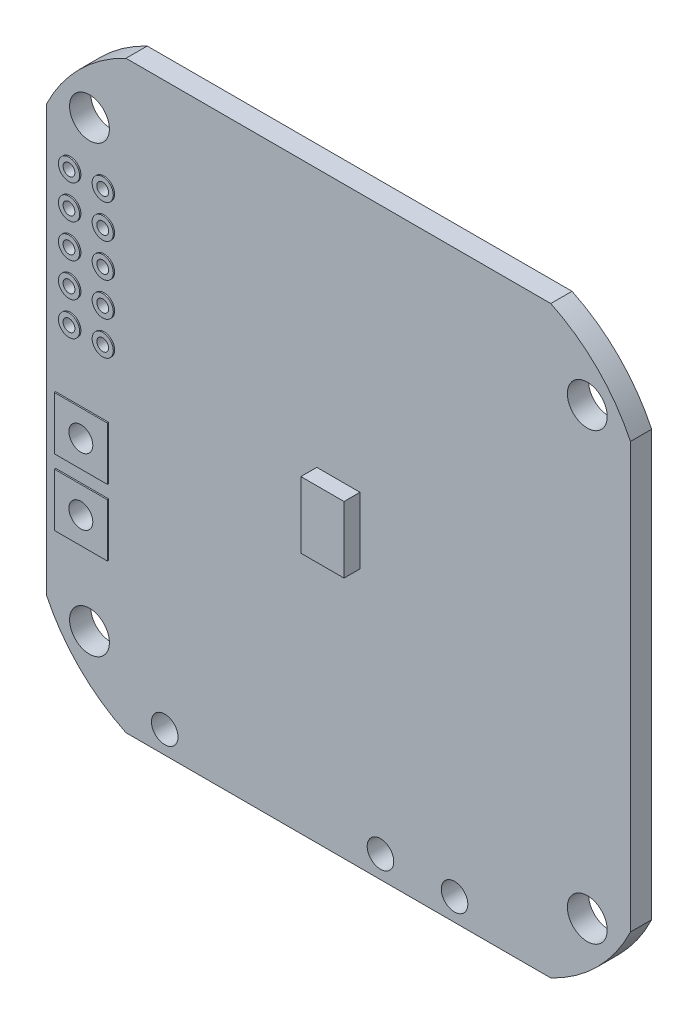
SolidWorks part; units mm, degrees
material "6061-T6 (SS)"
ref_plane "Alzado" through (0, 0, 0) normal (0, 0, 1) x (1, 0, 0)
ref_plane "Planta" through (0, 0, 0) normal (0, 1, 0) x (1, 0, 0)
ref_plane "Vista lateral" through (0, 0, 0) normal (1, 0, 0) x (0, 0, -1)
sketch "Croquis1" plane through (0, 0, 0) normal (0, 0, 1) x (1, 0, 0)
  line L0 (-22, 16) -> (-22, -16)
  line L1 (0, 0) -> (0, -6.2515) construction
  line L2 (22, 16) -> (22, -16)
  line L3 (-16, -22) -> (16, -22)
  line L4 (0, 0) -> (8.2976, 0) construction
  line L5 (-16, 22) -> (16, 22)
  arc A0 (-16, 22) -> (-22, 16) centre (-10.4982, 10.4982) ccw
  arc A2 (16, -22) -> (22, -16) centre (10.4982, -10.4982) ccw
  arc A3 (-22, -16) -> (-16, -22) centre (-10.4982, -10.4982) ccw
  arc A7 (22, 16) -> (16, 22) centre (10.4982, 10.4982) ccw
  point P0 (0, 0)
  point P4 (-22, 0)
  point P13 (0, -22)
  dimension "D3" = 25.5
  dimension "D4" = 32
  dimension "D1" = 32
  dimension "D2" = 22
  dimension "D5" = 22
extrude "Saliente-Extruir1" add sketch "Croquis1" along normal mid plane 1.6
sketch "Croquis2" plane through (0, 0, 0.8) normal (0, 0, 1) x (1, 0, 0)
  line L1 (18.75, -16.75) -> (-18.75, -16.75) construction
  line L2 (18.75, -16.75) -> (18.75, 16.75) construction
  line L3 (18.75, 16.75) -> (-18.75, 16.75) construction
  line L4 (-18.75, -16.75) -> (-18.75, 16.75) construction
  line L5 (18.75, -16.75) -> (-18.75, 16.75) construction
  line L6 (18.75, 16.75) -> (-18.75, -16.75) construction
  circle A0 centre (-18.75, 16.75) radius 1.5
  circle A1 centre (18.75, 16.75) radius 1.5
  circle A2 centre (18.75, -16.75) radius 1.5
  circle A3 centre (-18.75, -16.75) radius 1.5
  point P0 (0, 0)
  dimension "D1" = 3
  dimension "D2" = 37.5
  dimension "D3" = 33.5
extrude "Cortar-Extruir1" cut sketch "Croquis2" against normal through all
sketch "Croquis3" plane through (0, 0, 0.8) normal (0, 0, 1) x (1, 0, 0)
  line L1 (-1.625, 2.5) -> (1.625, 2.5)
  line L2 (-1.625, 2.5) -> (-1.625, -2.5)
  line L3 (-1.625, -2.5) -> (1.625, -2.5)
  line L4 (1.625, 2.5) -> (1.625, -2.5)
  line L5 (-1.625, 2.5) -> (1.625, -2.5) construction
  line L6 (-1.625, -2.5) -> (1.625, 2.5) construction
  point P0 (0, 0)
  dimension "D1" = 5
  dimension "D2" = 3.25
extrude "Saliente-Extruir2" add sketch "Croquis3" along normal blind 1.2
sketch "Croquis4" plane through (0, 0, -0.8) normal (0, 0, -1) x (-1, 0, 0)
  line L0 (22, 16) -> (22, -16) construction
  line L1 (-16, 22) -> (16, 22) construction
  circle A0 centre (17.653, 12.7) radius 0.445
  circle A1 centre (20.193, 12.7) radius 0.445
  circle A2 centre (20.193, 10.16) radius 0.445
  circle A3 centre (20.193, 7.62) radius 0.445
  circle A4 centre (20.193, 5.08) radius 0.445
  circle A5 centre (20.193, 2.54) radius 0.445
  circle A6 centre (17.653, 10.16) radius 0.445
  circle A7 centre (17.653, 7.62) radius 0.445
  circle A8 centre (17.653, 5.08) radius 0.445
  circle A9 centre (17.653, 2.54) radius 0.445
  dimension "D1" = 0.89
  dimension "D3" = 1.807
  dimension "D4" = 9.3
  dimension "D2" = 5
extrude "Cortar-Extruir2" cut sketch "Croquis4" against normal through all
sketch "Croquis5" plane through (0, 0, 0) normal (0, 0, 1) x (1, 0, 0)
  line L0 (-16, -22) -> (16, -22) construction
  line L1 (-17.3, -2.4) -> (-21.3, -2.4)
  line L2 (-17.3, -2.4) -> (-17.3, -6.4)
  line L3 (-17.3, -6.4) -> (-21.3, -6.4)
  line L4 (-21.3, -2.4) -> (-21.3, -6.4)
  line L5 (-17.3, -2.4) -> (-21.3, -6.4) construction
  line L6 (-17.3, -6.4) -> (-21.3, -2.4) construction
  line L7 (-17.3, -7.4) -> (-21.3, -7.4)
  line L8 (-17.3, -7.4) -> (-17.3, -11.4)
  line L9 (-17.3, -11.4) -> (-21.3, -11.4)
  line L10 (-21.3, -7.4) -> (-21.3, -11.4)
  line L11 (-17.3, -7.4) -> (-21.3, -11.4) construction
  line L12 (-17.3, -11.4) -> (-21.3, -7.4) construction
  line L13 (-22, 16) -> (-22, -16) construction
  circle A0 centre (-17.653, 2.54) radius 0.7974
  circle A1 centre (-20.193, 2.54) radius 0.7974
  circle A2 centre (-20.193, 5.08) radius 0.7974
  circle A3 centre (-17.653, 5.08) radius 0.7974
  circle A4 centre (-17.653, 7.62) radius 0.7974
  circle A5 centre (-17.653, 10.16) radius 0.7974
  circle A6 centre (-20.193, 7.62) radius 0.7974
  circle A7 centre (-20.193, 10.16) radius 0.7974
  circle A8 centre (-17.653, 12.7) radius 0.7974
  circle A9 centre (-20.193, 12.7) radius 0.7974
  circle A10 centre (-17.653, 12.7) radius 0.445
  circle A11 centre (-20.193, 12.7) radius 0.445
  circle A12 centre (-20.193, 10.16) radius 0.445
  circle A13 centre (-17.653, 10.16) radius 0.445
  circle A14 centre (-17.653, 7.62) radius 0.445
  circle A15 centre (-20.193, 7.62) radius 0.445
  circle A16 centre (-20.193, 5.08) radius 0.445
  circle A17 centre (-17.653, 5.08) radius 0.445
  circle A18 centre (-17.653, 2.54) radius 0.445
  circle A19 centre (-20.193, 2.54) radius 0.445
  point P0 (-19.3, -4.4)
  point P5 (-19.3, -9.4)
  dimension "D1" = 4
  dimension "D2" = 4
  dimension "D3" = 5
  dimension "D4" = 4
  dimension "D5" = 4
  dimension "D6" = 12.6
  dimension "D7" = 2.7
extrude "Saliente-Extruir3" add sketch "Croquis5" along normal mid plane 1.8
sketch "Croquis6" plane through (0, 0, -0.9) normal (0, 0, -1) x (-1, 0, 0)
  line L0 (21.3, -2.4) -> (21.3, -6.4) construction
  line L1 (21.3, -7.4) -> (21.3, -11.4) construction
  circle A0 centre (19.3, -4.4) radius 0.9
  circle A1 centre (19.3, -9.4) radius 0.9
  point P6 (21.3, -4.4)
  point P9 (21.3, -9.4)
  dimension "D1" = 1.8
extrude "Cortar-Extruir3" cut sketch "Croquis6" against normal through all both and the other way through all
sketch "Croquis7" plane through (0, 0, -0.8) normal (0, 0, -1) x (-1, 0, 0)
  line L0 (16, -22) -> (-16, -22) construction
  line L1 (22, 16) -> (22, -16) construction
  circle A0 centre (-8.75, -20.32) radius 1
  circle A1 centre (-3.17, -20.32) radius 1
  circle A2 centre (13.08, -20.32) radius 1
  dimension "D1" = 2
  dimension "D2" = 1.68
  dimension "D3" = 5.58
  dimension "D4" = 16.25
  dimension "D5" = 8.92
extrude "Cortar-Extruir4" cut sketch "Croquis7" against normal blind 10
sketch "Croquis8" plane through (0, 0, -0.8) normal (0, 0, -1) x (-1, 0, 0)
  line L0 (-22, -16) -> (-22, 16) construction
  line L1 (-20.5, 13.185) -> (-17.5, 13.185)
  line L2 (-20.5, 13.185) -> (-20.5, 10.685)
  line L3 (-20.5, 10.685) -> (-17.5, 10.685)
  line L4 (-17.5, 13.185) -> (-17.5, 10.685)
  line L5 (-20.5, 10.185) -> (-17.5, 10.185)
  line L6 (-20.5, 10.185) -> (-20.5, 7.685)
  line L7 (-20.5, 7.685) -> (-17.5, 7.685)
  line L8 (-17.5, 10.185) -> (-17.5, 7.685)
  line L9 (-16, 22) -> (16, 22) construction
  point P8 (-19, 7.685)
  point P11 (-20.5, 11.935)
  point P12 (-20.5, 8.935)
  dimension "D1" = 3
  dimension "D2" = 3
  dimension "D3" = 2.5
  dimension "D4" = 3
  dimension "D5" = 8.815
extrude "Saliente-Extruir4" add sketch "Croquis8" along normal blind 1.2
sketch "Croquis9" plane through (0, 0, -2) normal (0, 0, -1) x (-1, 0, 0)
  line L0 (-17.5, 13.185) -> (-20.5, 13.185) construction
  line L1 (-17.5, 7.685) -> (-17.5, 10.185) construction
  line L2 (-17.5, 10.685) -> (-17.5, 13.185) construction
  circle A0 centre (-19, 11.935) radius 0.75
  circle A1 centre (-19, 8.935) radius 0.75
  point P7 (-19, 13.185)
  point P10 (-17.5, 8.935)
  point P14 (-17.5, 11.935)
  dimension "D1" = 1.5
extrude "Saliente-Extruir5" add sketch "Croquis9" along normal blind 0.8
sketch "Croquis10" plane through (0, 0, -0.8) normal (0, 0, -1) x (-1, 0, 0)
  line L0 (-22, -16) -> (-22, 16) construction
  line L1 (-16, -14.25) -> (-11, -14.25)
  line L2 (-16, -14.25) -> (-16, -19.25)
  line L3 (-16, -19.25) -> (-11, -19.25)
  line L4 (-11, -14.25) -> (-11, -19.25)
  line L5 (16, -22) -> (-16, -22) construction
  line L6 (11.25, -12.2) -> (16.25, -12.2)
  line L7 (11.25, -12.2) -> (11.25, -17.2)
  line L8 (11.25, -17.2) -> (16.25, -17.2)
  line L9 (16.25, -12.2) -> (16.25, -17.2)
  line L10 (5.8877, -14.25) -> (10.8877, -14.25)
  line L11 (5.8877, -14.25) -> (5.8877, -19.25)
  line L12 (5.8877, -19.25) -> (10.8877, -19.25)
  line L13 (10.8877, -14.25) -> (10.8877, -19.25)
  line L14 (0.4343, -14.25) -> (5.4343, -14.25)
  line L15 (0.4343, -14.25) -> (0.4343, -19.25)
  line L16 (0.4343, -19.25) -> (5.4343, -19.25)
  line L17 (5.4343, -14.25) -> (5.4343, -19.25)
  line L18 (22, 16) -> (22, -16) construction
  line L19 (-4.9483, -12.2) -> (0.0517, -12.2)
  line L20 (-4.9483, -12.2) -> (-4.9483, -17.2)
  line L21 (-4.9483, -17.2) -> (0.0517, -17.2)
  line L22 (0.0517, -12.2) -> (0.0517, -17.2)
  line L23 (-10.5433, -12.2) -> (-5.5433, -12.2)
  line L24 (-10.5433, -12.2) -> (-10.5433, -17.2)
  line L25 (-10.5433, -17.2) -> (-5.5433, -17.2)
  line L26 (-5.5433, -12.2) -> (-5.5433, -17.2)
  dimension "D1" = 5
  dimension "D2" = 5
  dimension "D3" = 6
  dimension "D4" = 2.75
  dimension "D5" = 5
  dimension "D6" = 5
  dimension "D7" = 5
  dimension "D8" = 5
  dimension "D9" = 5
  dimension "D10" = 5
  dimension "D11" = 5.75
  dimension "D12" = 4.8
  dimension "D13" = 5
  dimension "D14" = 5
  dimension "D15" = 5
  dimension "D16" = 5
extrude "Saliente-Extruir6" add sketch "Croquis10" along normal blind 0.9
sketch "Croquis11" plane through (0, 0, -0.8) normal (0, 0, -1) x (-1, 0, 0)
  line L0 (-13.6529, -19.5225) -> (-10.4593, -19.5225)
  line L1 (-10.4593, -19.5225) -> (-9.8124, -18.8756)
  line L2 (-9.8124, -18.8756) -> (-7.529, -18.8756)
  line L3 (-7.529, -18.8756) -> (-7.1476, -19.257)
  line L4 (-7.1476, -19.257) -> (-7.1476, -21.3437)
  line L5 (-7.1476, -21.3437) -> (-7.529, -21.7251)
  line L6 (-7.529, -21.7251) -> (-13.8301, -21.7251)
  line L7 (-13.8301, -21.7251) -> (-14.1414, -21.4138)
  line L8 (-14.1414, -21.4138) -> (-14.1414, -20.011)
  line L9 (-14.1414, -20.011) -> (-13.6529, -19.5225)
  line L10 (8.1723, -19.5225) -> (11.1983, -19.5225)
  line L11 (11.1983, -19.5225) -> (12.0225, -18.6983)
  line L12 (12.0225, -18.6983) -> (14.2962, -18.6983)
  line L13 (14.2962, -18.6983) -> (14.7785, -19.1806)
  line L14 (14.7785, -19.1806) -> (14.7785, -21.2429)
  line L15 (14.7785, -21.2429) -> (14.2962, -21.7251)
  line L16 (14.2962, -21.7251) -> (7.9951, -21.7251)
  line L17 (7.9951, -21.7251) -> (7.6839, -21.4138)
  line L18 (7.6839, -21.4138) -> (7.6839, -20.011)
  line L19 (7.6839, -20.011) -> (8.1723, -19.5225)
  line L20 (2.2631, -20.011) -> (1.7746, -19.5225)
  line L21 (2.2631, -21.4138) -> (2.2631, -20.011)
  line L22 (1.9518, -21.7251) -> (2.2631, -21.4138)
  line L23 (-4.3493, -21.7251) -> (1.9518, -21.7251)
  line L24 (-4.7307, -21.3437) -> (-4.3493, -21.7251)
  line L25 (-4.7307, -19.257) -> (-4.7307, -21.3437)
  line L26 (-4.3493, -18.8756) -> (-4.7307, -19.257)
  line L27 (-2.0659, -18.8756) -> (-4.3493, -18.8756)
  line L28 (-1.4189, -19.5225) -> (-2.0659, -18.8756)
  line L29 (1.7746, -19.5225) -> (-1.4189, -19.5225)
  line L30 (-5.9391, -18.0693) -> (-5.9391, -23.1735) construction
  circle A0 centre (-8.75, -20.32) radius 1
  circle A1 centre (-3.17, -20.32) radius 1
  circle A2 centre (13.08, -20.32) radius 1
extrude "Saliente-Extruir7" add sketch "Croquis11" along normal blind 0.1
sketch "Croquis12" plane through (0, 0, -0.8) normal (0, 0, -1) x (-1, 0, 0)
  line L0 (-17.166, -2.5014) -> (-10.8812, -8.7862)
  line L1 (-17.166, -2.5014) -> (-10.8812, 3.7834)
  line L2 (-10.8812, -8.7862) -> (-4.5964, -2.5014)
  line L3 (-10.8812, 3.7834) -> (-4.5964, -2.5014)
  line L4 (16, -22) -> (-16, -22) construction
  point P0 (-10.8812, 3.7834)
  dimension "D1" = 45
extrude "Saliente-Extruir8" add sketch "Croquis12" along normal blind 0.75
